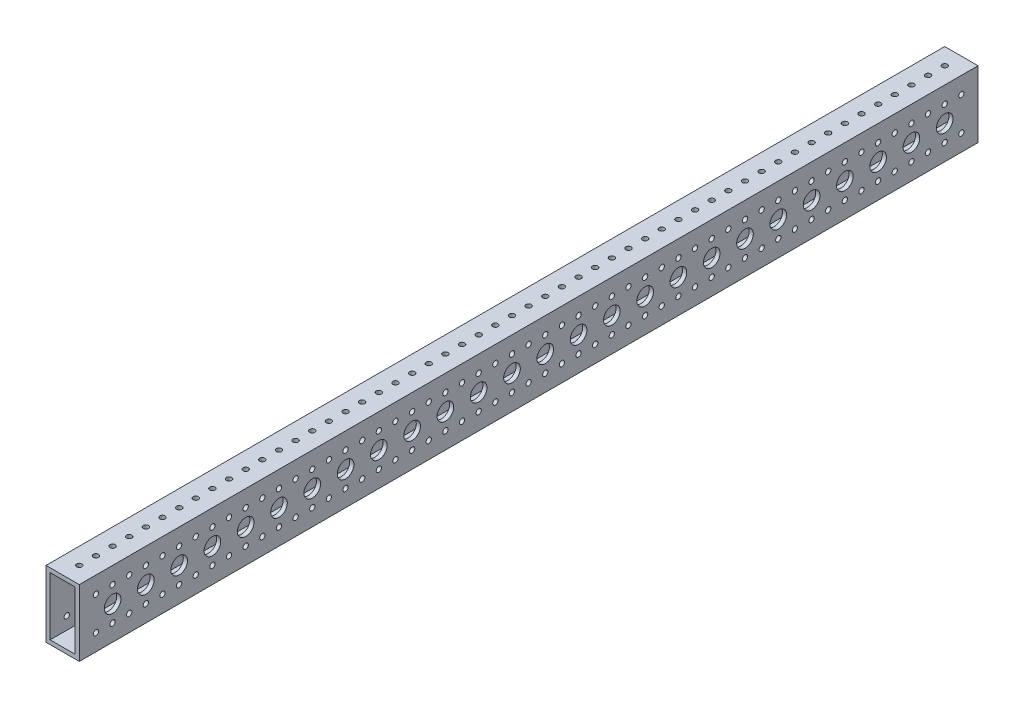
SolidWorks part; units mm, degrees
material "6061 Alloy"
ref_plane "Front Plane" through (0, 0, 0) normal (0, 0, 1) x (1, 0, 0)
ref_plane "Top Plane" through (0, 0, 0) normal (0, 1, 0) x (1, 0, 0)
ref_plane "Right Plane" through (0, 0, 0) normal (1, 0, 0) x (0, 0, -1)
sketch "Sketch1" plane through (0, 0, 0) normal (0, 0, 1) x (1, 0, 0)
  line L1 (12.7, 25.4) -> (-12.7, 25.4)
  line L2 (12.7, 25.4) -> (12.7, -25.4)
  line L3 (12.7, -25.4) -> (-12.7, -25.4)
  line L4 (-12.7, 25.4) -> (-12.7, -25.4)
  line L5 (12.7, 25.4) -> (-12.7, -25.4) construction
  line L6 (12.7, -25.4) -> (-12.7, 25.4) construction
  point P0 (0, 0)
  dimension "D1" = 25.4
  dimension "D2" = 50.8
extrude "Boss-Extrude1" add sketch "Sketch1" along normal blind 685.8
shell "Shell1" thickness 3.175
hole_wizard "#21 (0.159) Diameter Hole1" positions "Sketch2" profile "Sketch3" hole size "#21" standard "ANSI Inch" end condition through all
sketch "Sketch2" plane through (0, 25.4, 0) normal (0, 1, 0) x (1, 0, 0)
  line L0 (12.7, 0) -> (-12.7, 0) construction
  line L1 (12.7, -685.8) -> (12.7, 0) construction
  point P0 (0, -12.7)
  dimension "D1" = 12.7
  dimension "D2" = 12.7
sketch "Sketch3" plane through (0, 25.4, 12.7) normal (1, 0, 0) x (0, 0, 1)
  line L0 (0, 0) -> (0, 50.8)
  line L1 (0, 50.8) -> (2.0193, 50.8)
  line L2 (2.0193, 50.8) -> (2.0193, 0)
  line L5 (2.0193, 0) -> (0, 0)
  line L11 (0, -6.35) -> (0, 107.95) construction
  dimension "Thru Hole Dia." = 4.0386
  dimension "Thru Hole Depth" = 50.8
pattern_linear "LPattern1" count 53 spacing 12.7 along (0, 0, 1) of "#21 (0.159) Diameter Hole1"
hole_wizard "#21 (0.159) Diameter Hole2" positions "Sketch4" profile "Sketch5" hole size "#21" standard "ANSI Inch" end condition through all
sketch "Sketch4" plane through (-12.7, 0, 0) normal (-1, 0, 0) x (0, 0, 1)
  line L0 (685.8, 25.4) -> (0, 25.4) construction
  line L1 (0, 25.4) -> (0, -25.4) construction
  point P0 (12.7, 12.7)
  dimension "D1" = 12.7
  dimension "D2" = 12.7
sketch "Sketch5" plane through (-12.7, 12.7, 12.7) normal (0, 1, 0) x (0, 0, 1)
  line L0 (0, 0) -> (0, 25.4)
  line L1 (0, 25.4) -> (2.0193, 25.4)
  line L2 (2.0193, 25.4) -> (2.0193, 0)
  line L5 (2.0193, 0) -> (0, 0)
  line L11 (0, -6.35) -> (0, 107.95) construction
  dimension "Thru Hole Dia." = 4.0386
  dimension "Thru Hole Depth" = 25.4
pattern_linear "LPattern2" count 53 spacing 12.7 along (0, 0, 1) count 2 spacing 25.4 along (0, -1, 0) of "#21 (0.159) Diameter Hole2"
hole_wizard "1/2 (0.5) Diameter Hole1" positions "Sketch6" profile "Sketch7" hole size "1/2" standard "ANSI Inch" end condition through all
sketch "Sketch6" plane through (-12.7, 0, 0) normal (-1, 0, 0) x (0, 0, 1)
  line L0 (685.8, 25.4) -> (0, 25.4) construction
  line L1 (0, 25.4) -> (0, -25.4) construction
  point P0 (25.4, 0)
  dimension "D1" = 25.4
  dimension "D2" = 25.4
sketch "Sketch7" plane through (-12.7, 0, 25.4) normal (0, 1, 0) x (0, 0, 1)
  line L0 (0, 0) -> (0, 25.4)
  line L1 (0, 25.4) -> (6.35, 25.4)
  line L2 (6.35, 25.4) -> (6.35, 0)
  line L5 (6.35, 0) -> (0, 0)
  line L11 (0, -6.35) -> (0, 107.95) construction
  dimension "Thru Hole Dia." = 12.7
  dimension "Thru Hole Depth" = 25.4
pattern_linear "LPattern3" count 26 spacing 25.4 along (0, 0, 1) of "1/2 (0.5) Diameter Hole1"
equation "\"Length\"= 27"
equation "\"D1@Boss-Extrude1\"= \"Length\""
